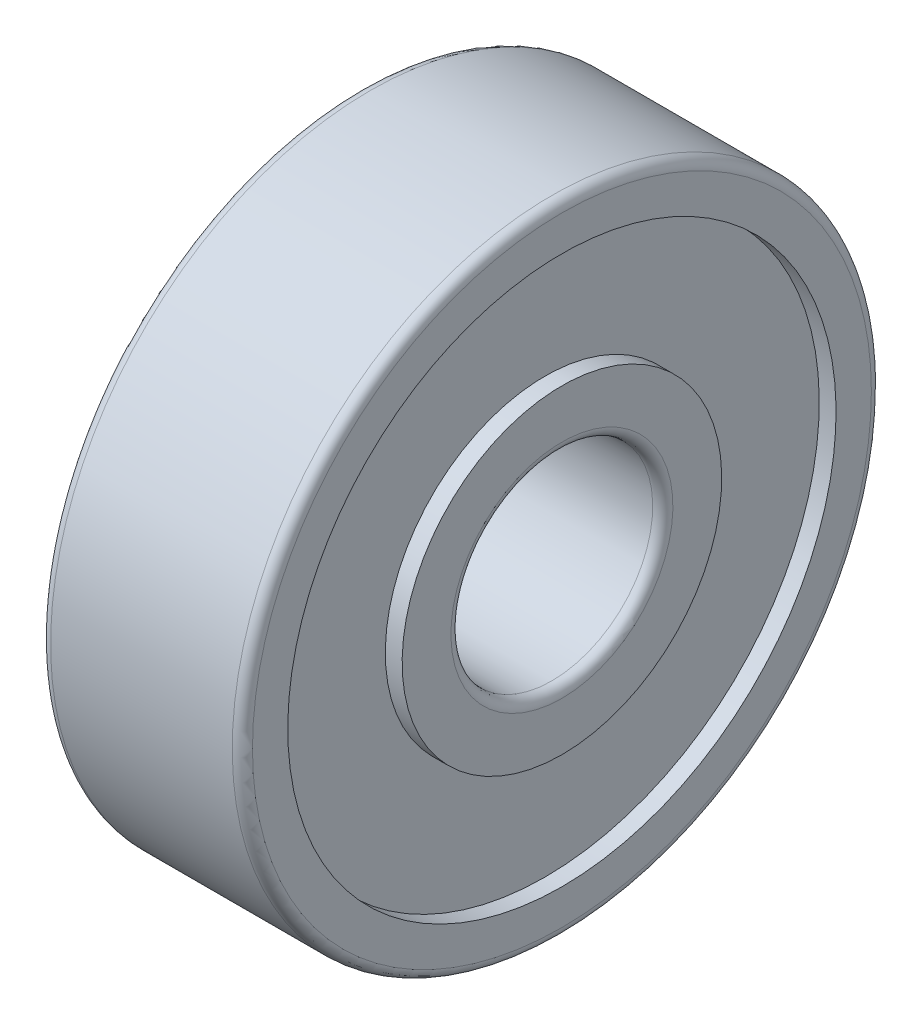
SolidWorks part; units mm, degrees
ref_plane "Front Plane" through (0, 0, 0) normal (0, 0, 1) x (1, 0, 0)
ref_plane "Top Plane" through (0, 0, 0) normal (0, 1, 0) x (1, 0, 0)
ref_plane "Right Plane" through (0, 0, 0) normal (1, 0, 0) x (0, 0, -1)
sketch "Sketch1" plane through (0, 0, 0) normal (0, 0, 1) x (1, 0, 0)
  line L0 (0, 0) -> (6, 0) construction
  line L1 (0, 3) -> (6, 3)
  line L2 (0, 9.5) -> (6, 9.5)
  line L3 (0, 9.5) -> (0, 8.15)
  line L4 (0, 8.15) -> (0.5, 8.15)
  line L5 (6, 9.5) -> (6, 8.15)
  line L6 (0.5, 8.15) -> (0.5, 4.75)
  line L7 (0.5, 4.75) -> (0, 4.75)
  line L8 (0, 4.75) -> (0, 3)
  line L9 (6, 8.15) -> (5.5, 8.15)
  line L10 (5.5, 8.15) -> (5.5, 4.75)
  line L11 (5.5, 4.75) -> (6, 4.75)
  line L12 (6, 4.75) -> (6, 3)
  dimension "D" = 19
  dimension "B" = 6
  dimension "D_s" = 6
  dimension "MSM_1" = 16.3
  dimension "MSM_2" = 9.5
  dimension "MSM_3" = 0.5
revolve "Revolve1" add sketch "Sketch1" angle 360 about L0
fillet "Fillet1" radius 0.3 2 edges at (6, -9.5, 0) (0, -9.5, 0)
fillet "Fillet2" radius 0.3 2 edges at (6, -3, 0) (0, -3, 0)
